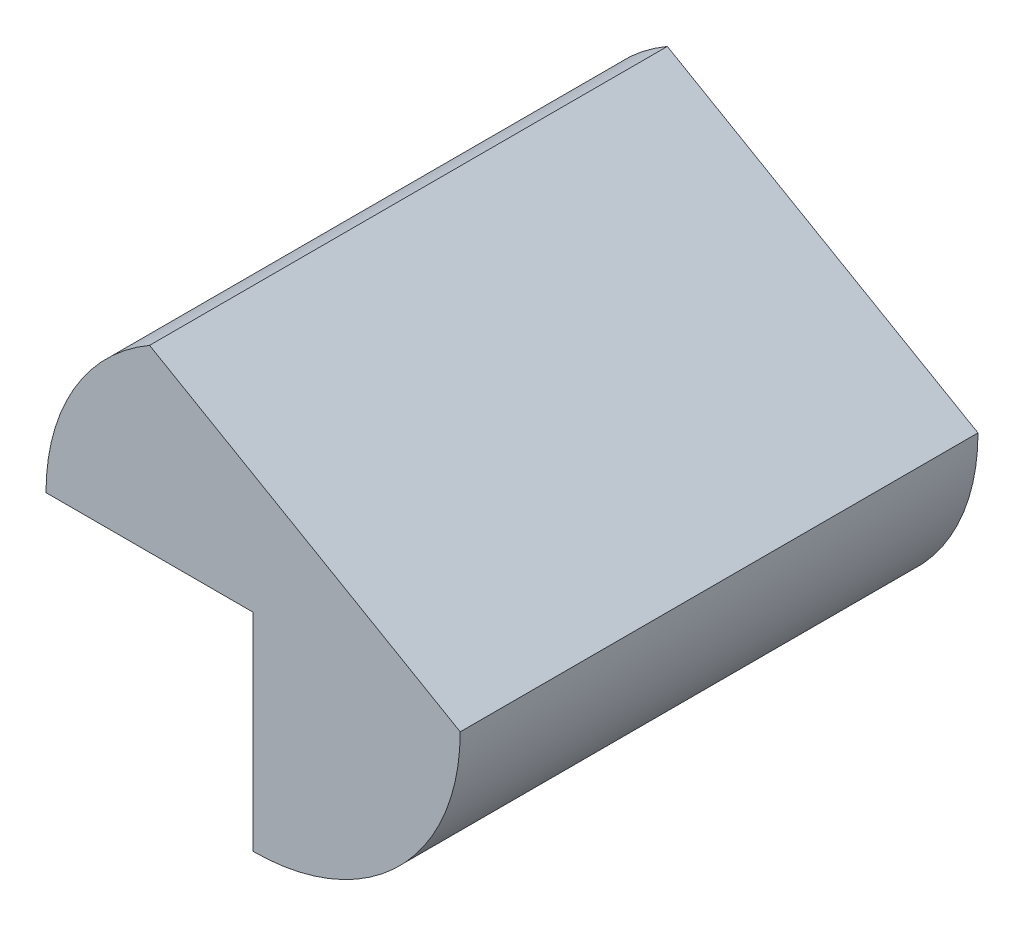
SolidWorks part; units mm, degrees
ref_plane "Front Plane" through (0, 0, 0) normal (0, 0, 1) x (1, 0, 0)
ref_plane "Top Plane" through (0, 0, 0) normal (0, 1, 0) x (1, 0, 0)
ref_plane "Right Plane" through (0, 0, 0) normal (1, 0, 0) x (0, 0, -1)
sketch "Sketch1" plane through (0, 0, 0) normal (0, 0, 1) x (1, 0, 0)
  line L0 (-10, 0) -> (0, 0)
  line L1 (0, 0) -> (0, -10)
  line L2 (-5, 8.6603) -> (10, 0)
  arc A0 (0, -10) -> (10, 0) centre (0, 0) ccw
  arc A1 (-10, 0) -> (-5, 8.6603) centre (0, 0) cw
  point P5 (-5, 0)
  dimension "D1" = 10
  dimension "D2" = 10
extrude "Boss-Extrude1" add sketch "Sketch1" along normal blind 25
